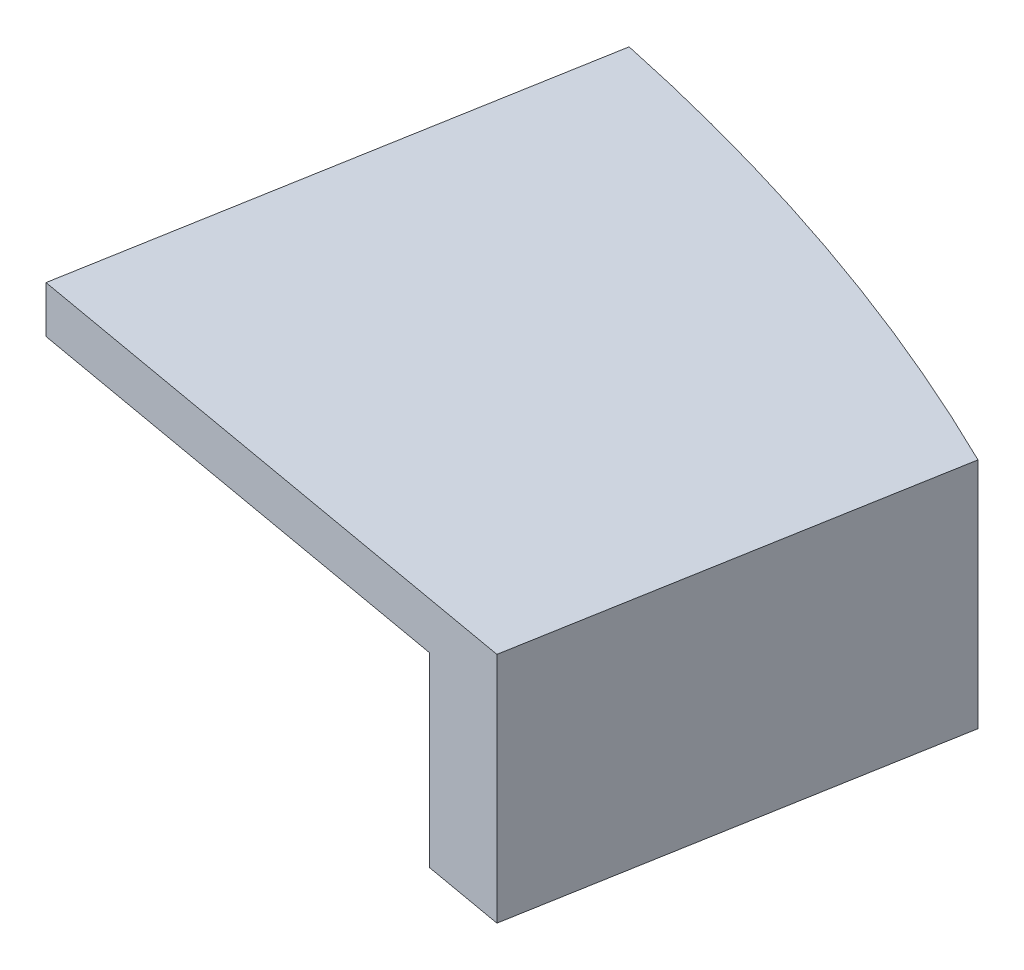
SolidWorks part; units mm, degrees
ref_plane "Front Plane" through (0, 0, 0) normal (0, 0, 1) x (1, 0, 0)
ref_plane "Top Plane" through (0, 0, 0) normal (0, 1, 0) x (1, 0, 0)
ref_plane "Right Plane" through (0, 0, 0) normal (1, 0, 0) x (0, 0, -1)
ref_plane "Plane1" through (0, 12.5277, 0) normal (0, 1, 0) x (1, 0, 0)
sketch "Sketch1" plane through (0, 0, 0) normal (0, 1, 0) x (1, 0, 0)
  ellipse E0 centre (0, 0) end of major axis (-75, 0) minor radius 65 construction
  point P1 (0, 0)
  point P7 (0, 65)
  point P9 (20.7999, 62.4503)
  point P10 (0, 0)
  dimension "D1" = 130
  dimension "D2" = 150
sketch "Sketch23" plane through (0, 12.5277, 0) normal (0, 1, 0) x (1, 0, 0)
  line L0 (17.8631, 63.1294) -> (14.7182, 45.2935)
  line L1 (14.7182, 45.2935) -> (34.4143, 41.8205)
  line L2 (34.4143, 41.8205) -> (37.0089, 56.5352)
  line L3 (36.4656, 53.4538) -> (37.0089, 56.5352) construction
  line L4 (17.8631, 63.1294) -> (17.3419, 60.1732) construction
  line L6 (16.4546, 55.1416) -> (17.3419, 60.1732) construction
  line L7 (34.4143, 41.8205) -> (-9.902, 49.6347) construction
  ellipse E0 centre (0, 0) end of major axis (-75, 0) minor radius 65 construction
  ellipse E1 centre (0, 0) end of major axis (-75, 0) minor radius 65 (37.0089, 56.5352) -> (17.8631, 63.1294) ccw
  point P10 (37.0089, 56.5352)
  point P17 (31.5682, 38.1147)
  point P18 (17.8631, 63.1294)
  point P23 (17.8631, 63.1294)
extrude "Boss-Extrude7" add sketch "Sketch23" against normal blind 1.68
sketch "Sketch24" plane through (0, 10.8477, 0) normal (0, -1, 0) x (1, 0, 0)
  line L0 (16.9061, -57.7021) -> (33.6479, -54.75) construction
  line L1 (16.9061, -57.7021) -> (33.6479, -54.75)
  line L2 (17.8631, -63.1294) -> (14.7182, -45.2935) construction
  line L3 (17.8631, -63.1294) -> (16.9061, -57.7021)
  line L4 (34.4143, -41.8205) -> (37.0089, -56.5352) construction
  line L5 (34.4143, -41.8205) -> (37.0089, -56.5352)
  line L6 (14.7182, -45.2935) -> (34.4143, -41.8205) construction
  line L7 (31.4599, -42.3415) -> (34.4143, -41.8205)
  line L8 (33.6479, -54.75) -> (32.0156, -45.4929) construction
  line L9 (33.6479, -54.75) -> (31.4599, -42.3415)
  ellipse E0 centre (0, 0) end of major axis (-75, 0) minor radius 65 (17.8631, -63.1294) -> (37.0089, -56.5352) ccw construction
  ellipse E1 centre (0, 0) end of major axis (-75, 0) minor radius 65 (17.8631, -63.1294) -> (37.0089, -56.5352) ccw
extrude "Boss-Extrude8" add sketch "Sketch24" along normal up to surface (6.6954 mm away)
